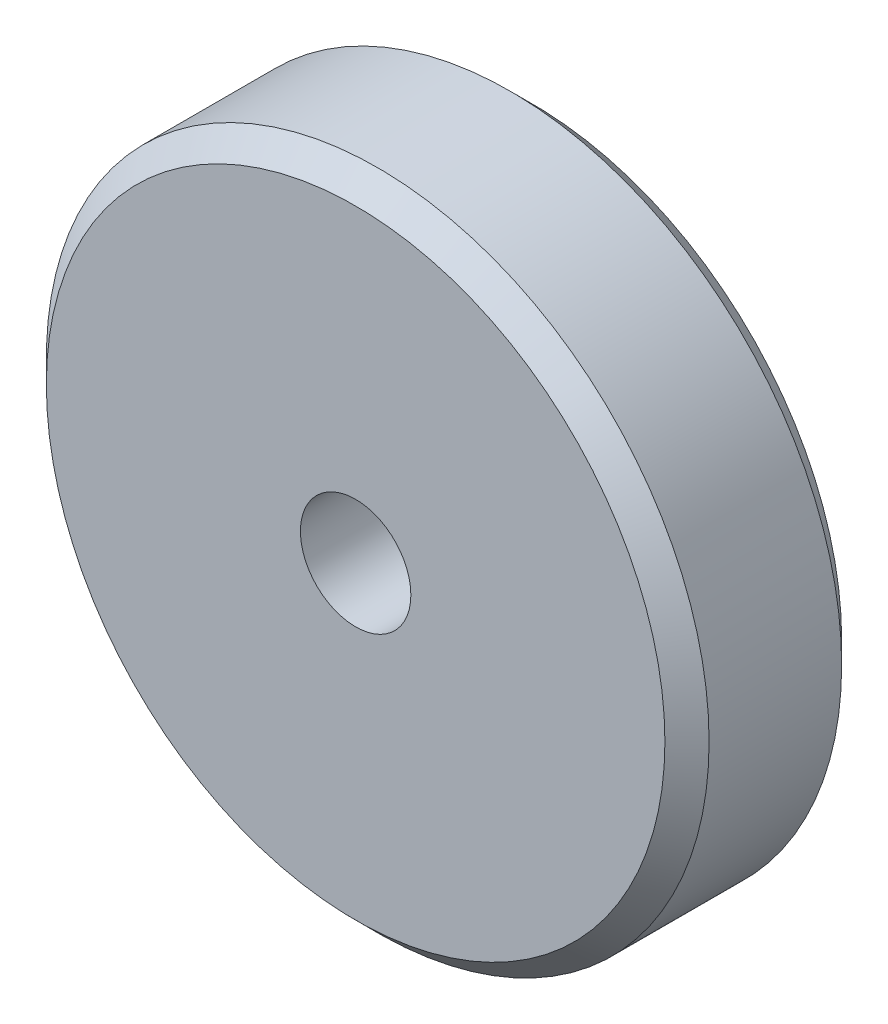
SolidWorks part; units mm, degrees
ref_plane "Front Plane" through (0, 0, 0) normal (0, 0, 1) x (1, 0, 0)
ref_plane "Top Plane" through (0, 0, 0) normal (0, 1, 0) x (1, 0, 0)
ref_plane "Right Plane" through (0, 0, 0) normal (1, 0, 0) x (0, 0, -1)
sketch "Sketch1" plane through (0, 0, 0) normal (0, 0, 1) x (1, 0, 0)
  circle A0 centre (0, 0) radius 2.5
  circle A1 centre (0, 0) radius 15
  dimension "D1" = 5
  dimension "D2" = 30
extrude "Boss-Extrude1" add sketch "Sketch1" along normal blind 8
chamfer "Chamfer1" distance 1 angle 45 2 edges at (15, 0, 0) (15, 0, 8)
